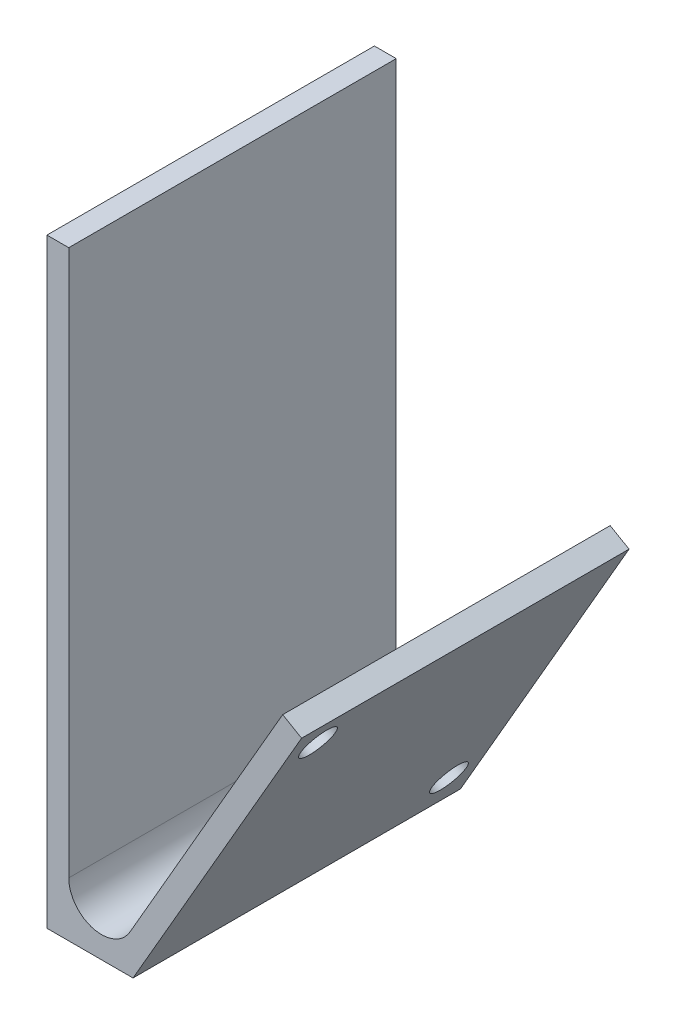
SolidWorks part; units mm, degrees
ref_plane "Plano frontal" through (0, 0, 0) normal (0, 0, 1) x (1, 0, 0)
ref_plane "Plano superior" through (0, 0, 0) normal (0, 1, 0) x (1, 0, 0)
ref_plane "Plano direito" through (0, 0, 0) normal (1, 0, 0) x (0, 0, -1)
sketch "Esboço1" plane through (0, 0, 0) normal (0, 0, 1) x (1, 0, 0)
  line L0 (0, 55) -> (0, 0)
  line L1 (0, 0) -> (7.8868, 0)
  line L2 (7.8868, 0) -> (23.3301, 26.7487)
  line L3 (23.3301, 26.7487) -> (21.5981, 27.7487)
  line L4 (21.5981, 27.7487) -> (7.5981, 3.5)
  line L5 (2, 5) -> (2, 55)
  line L6 (2, 55) -> (0, 55)
  line L7 (23.3301, 26.7487) -> (31.9904, 21.7487) construction
  line L8 (31.9904, 21.7487) -> (16.9904, -4.2321) construction
  line L9 (16.9904, -4.2321) -> (8.3301, 0.7679) construction
  arc A0 (7.5981, 3.5) -> (2, 5) centre (5, 5) cw
  point P9 (3.9434, 0)
  point P13 (7.5981, 0)
  dimension "D3" = 3
  dimension "D9" = 2
  dimension "D1" = 30
  dimension "D2" = 2
  dimension "D4" = 28
  dimension "D5" = 55
  dimension "D6" = 10
  dimension "D7" = 30
  dimension "D8" = 4.2321
extrude "Ressalto-extrusão1" add sketch "Esboço1" along normal blind 30
sketch "Esboço2" plane through (4.183, -2.4151, 0) normal (-0.866, 0.5, 0) x (0.5, 0.866, 0)
  line L0 (4.8301, 0) -> (34.8301, -30) construction
  line L2 (19.8301, -15) -> (34.8301, 0) construction
  line L3 (34.8301, -30) -> (34.8301, 0) construction
  line L4 (47.6314, 0) -> (0, 0) construction
  circle A0 centre (31.8301, -27) radius 1.6
  circle A1 centre (7.8301, -3) radius 1.6
  point P3 (50.0577, -7.2145)
  point P4 (43.0829, 0)
  point P15 (43.0829, -30)
  point P17 (12.9121, 0)
  dimension "D1" = 3.2
  dimension "D2" = 3
extrude "Corte-extrusão1" cut sketch "Esboço2" against normal blind 30
